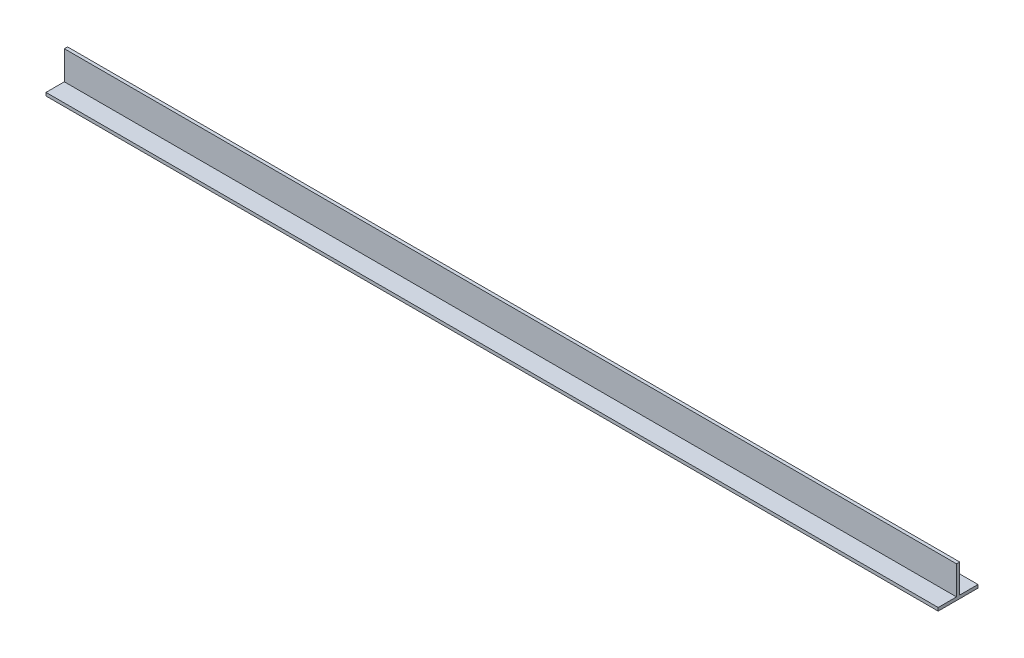
SolidWorks part; units mm, degrees
material "6061-T6 (SS)"
ref_plane "Front Plane" through (0, 0, 0) normal (0, 0, 1) x (1, 0, 0)
ref_plane "Top Plane" through (0, 0, 0) normal (0, 1, 0) x (1, 0, 0)
ref_plane "Right Plane" through (0, 0, 0) normal (1, 0, 0) x (0, 0, -1)
sketch "Sketch1" plane through (0, 0, 0) normal (1, 0, 0) x (0, 0, -1)
  line L0 (0.635, 0) -> (7.9375, 0)
  line L1 (-7.9375, 0) -> (-0.635, 0)
  line L2 (-7.9375, 0) -> (-7.9375, -1.27)
  line L3 (-7.9375, -1.27) -> (7.9375, -1.27)
  line L4 (7.9375, 0) -> (7.9375, -1.27)
  line L5 (-0.635, 11.43) -> (0.635, 11.43)
  line L6 (-0.635, 11.43) -> (-0.635, 0)
  line L8 (0.635, 11.43) -> (0.635, 0)
  dimension "D1" = 1.27
  dimension "D2" = 15.875
  dimension "D3" = 11.43
  dimension "D4" = 1.27
extrude "Boss-Extrude1" add sketch "Sketch1" along normal blind 355.6
sketch "Sketch2" plane through (0, 0, 0) normal (0, 1, 0) x (1, 0, 0)
  line L0 (0, 0.635) -> (0, 7.9375) construction
  line L1 (0, 4.2862) -> (355.6, 4.2862) construction
  line L2 (355.6, 7.9375) -> (355.6, 0.635) construction
  line L3 (25.4, 4.2862) -> (127, 4.2862) construction
  circle A0 centre (25.4, 4.2862) radius 2.1527
  circle A1 centre (127, 4.2862) radius 2.1526
  circle A2 centre (228.6, 4.2862) radius 2.1527
  circle A3 centre (330.2, 4.2862) radius 2.1527
  dimension "D2" = 4.3053
  dimension "D1" = 25.4
  dimension "D4" = 3.6513
  dimension "D3" = 101.6
extrude "Cut-Extrude1" cut sketch "Sketch2" against normal up to next
